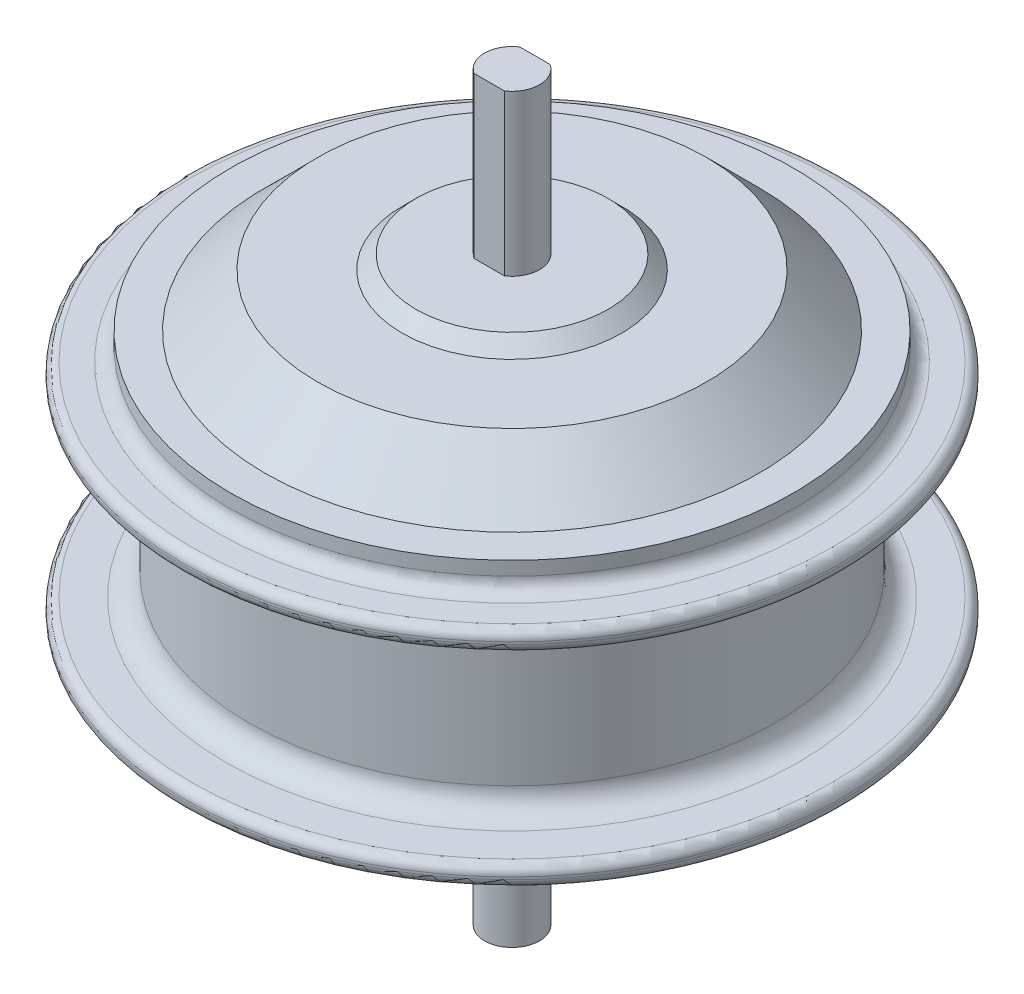
SolidWorks part; units mm, degrees
ref_plane "Спереди" through (0, 0, 0) normal (0, 0, 1) x (1, 0, 0)
ref_plane "Сверху" through (0, 0, 0) normal (0, 1, 0) x (1, 0, 0)
ref_plane "Справа" through (0, 0, 0) normal (1, 0, 0) x (0, 0, -1)
sketch "Эскиз1" plane through (0, 0, 0) normal (1, 0, 0) x (0, 0, -1)
  line L0 (0, -498.2504) -> (0, 24414.2701) construction
  line L1 (0, 80) -> (-6, 80)
  line L2 (-6, 80) -> (-6, 45)
  line L3 (-6, 45) -> (-21, 45)
  line L4 (-21, 45) -> (-24, 42)
  line L5 (-24, 42) -> (-42.5, 42)
  line L6 (-42.5, 42) -> (-54, 30.5)
  line L7 (-54, 30.5) -> (-61.5, 30.5)
  line L8 (-61.5, 30.5) -> (-61.5, 24.5)
  line L9 (-61.5, 24.5) -> (-72, 24.5)
  line L10 (-72, 24.5) -> (-72, 20)
  line L11 (-72, 20) -> (-57.5, 20)
  line L12 (-57.5, 20) -> (-57.5, -20)
  line L13 (-57.5, -20) -> (-72, -20)
  line L14 (-72, -20) -> (-72, -24.5)
  line L15 (-72, -24.5) -> (-61.5, -24.5)
  line L16 (-61.5, -24.5) -> (-61.5, -30.5)
  line L17 (-61.5, -30.5) -> (-54, -30.5)
  line L18 (-54, -30.5) -> (-42.5, -42)
  line L19 (-42.5, -42) -> (-26.65, -42)
  line L20 (-26.65, -42) -> (-26.65, -51)
  line L21 (-26.65, -51) -> (-6, -51)
  line L22 (-6, -51) -> (-6, -82)
  line L23 (-6, -82) -> (0, -82)
  line L24 (-57.5, 0) -> (0, 0) construction
  line L25 (0, 80) -> (0, -82)
  dimension "D1" = 12
  dimension "D2" = 144
  dimension "D3" = 115
  dimension "D4" = 53.3
  dimension "D5" = 123
  dimension "D6" = 123
  dimension "D7" = 108
  dimension "D8" = 108
  dimension "D9" = 85
  dimension "D10" = 85
  dimension "D11" = 48
  dimension "D12" = 42
  dimension "D13" = 35
  dimension "D14" = 3
  dimension "D15" = 4.5
  dimension "D16" = 40
  dimension "D17" = 31
  dimension "D18" = 9
  dimension "D19" = 6
  dimension "D20" = 6
revolve "Повернуть1" add sketch "Эскиз1" angle 360 about L25
fillet "Скругление1" radius 2 4 edges at (0, -24.5, 72) (0, -20, 72) (0, 20, 72) (0, 24.5, 72)
fillet "Скругление2" radius 5 2 edges at (0, 20, 57.5) (0, -20, 57.5)
fillet "Скругление3" radius 3 2 edges at (0, -24.5, 61.5) (0, 24.5, 61.5)
sketch "Эскиз2" plane through (0, 80, 0) normal (0, 1, 0) x (1, 0, 0)
  line L1 (-3.3166, 5) -> (3.3166, 5)
  line L3 (-3.3166, -5) -> (3.3166, -5)
  circle A0 centre (0, 0) radius 6 construction
  arc A1 (-3.3166, -5) -> (3.3166, -5) centre (0, 0) ccw
  arc A2 (3.3166, 5) -> (-3.3166, 5) centre (0, 0) ccw
  point P7 (0, 0)
  point P8 (0, 0)
  point P9 (0, 0)
  point P10 (0, 0)
  dimension "D1" = 10
extrude "Вырез-Вытянуть1" cut sketch "Эскиз2" against normal up to surface (35 mm away) up to face at (0, 45, 21)
